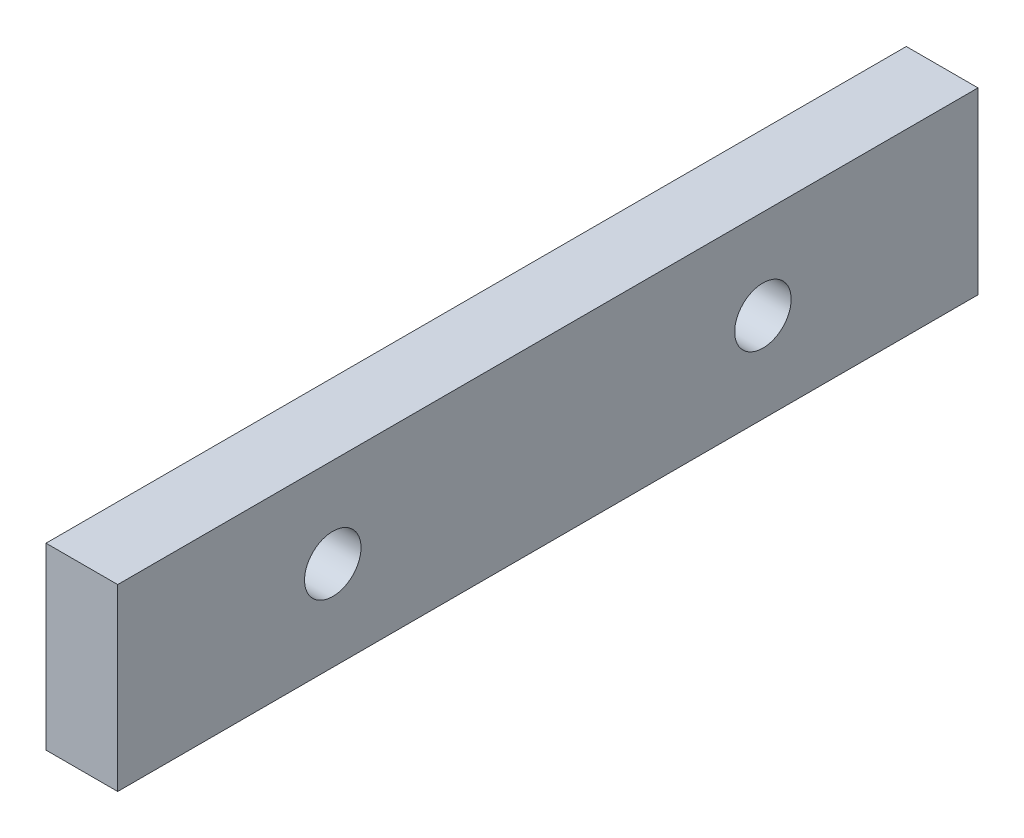
SolidWorks part; units mm, degrees
material "SS 304 (Default)"
ref_plane "Front Plane" through (0, 0, 0) normal (0, 0, 1) x (1, 0, 0)
ref_plane "Top Plane" through (0, 0, 0) normal (0, 1, 0) x (1, 0, 0)
ref_plane "Right Plane" through (0, 0, 0) normal (1, 0, 0) x (0, 0, -1)
sketch "Sketch1" plane through (0, 0, 0) normal (0, 0, 1) x (1, 0, 0)
  line L1 (-3.175, 7.9375) -> (3.175, 7.9375)
  line L2 (-3.175, 7.9375) -> (-3.175, -7.9375)
  line L3 (-3.175, -7.9375) -> (3.175, -7.9375)
  line L4 (3.175, 7.9375) -> (3.175, -7.9375)
  line L5 (-3.175, 7.9375) -> (3.175, -7.9375) construction
  line L6 (-3.175, -7.9375) -> (3.175, 7.9375) construction
  point P0 (0, 0)
  dimension "Width" = 6.35
  dimension "Height" = 15.875
extrude "Extrude1" add sketch "Sketch1" along normal mid plane 76.2
hole_wizard "M6x1.0 Tapped Hole1" positions "Sketch3" profile "Sketch2" tap size "M6x1.0" standard "Ansi Metric" end condition up to next
sketch "Sketch3" plane through (3.175, 0, 0) normal (1, 0, 0) x (0, 0, -1)
  line L0 (-19.05, 0) -> (19.05, 0) construction
  point P0 (-19.05, 0)
  point P1 (19.05, 0)
  point P10 (-44.45, 0)
  dimension "D1" = 38.1
sketch "Sketch2" plane through (3.175, 0, 19.05) normal (0, 1, 0) x (0, 0, -1)
  line L0 (0, 0) -> (0, 6.35)
  line L1 (0, 6.35) -> (2.5, 6.35)
  line L2 (2.5, 6.35) -> (2.5, 0)
  line L5 (2.5, 0) -> (0, 0)
  line L11 (0, -6.35) -> (0, 107.95) construction
  dimension "Thru Tap Drill Dia." = 5
  dimension "Thru Tap Drill Depth" = 6.35
cosmetic thread "Hole Thread1" parameters "D2"=6
cosmetic thread "Hole Thread2" parameters "D2"=6
